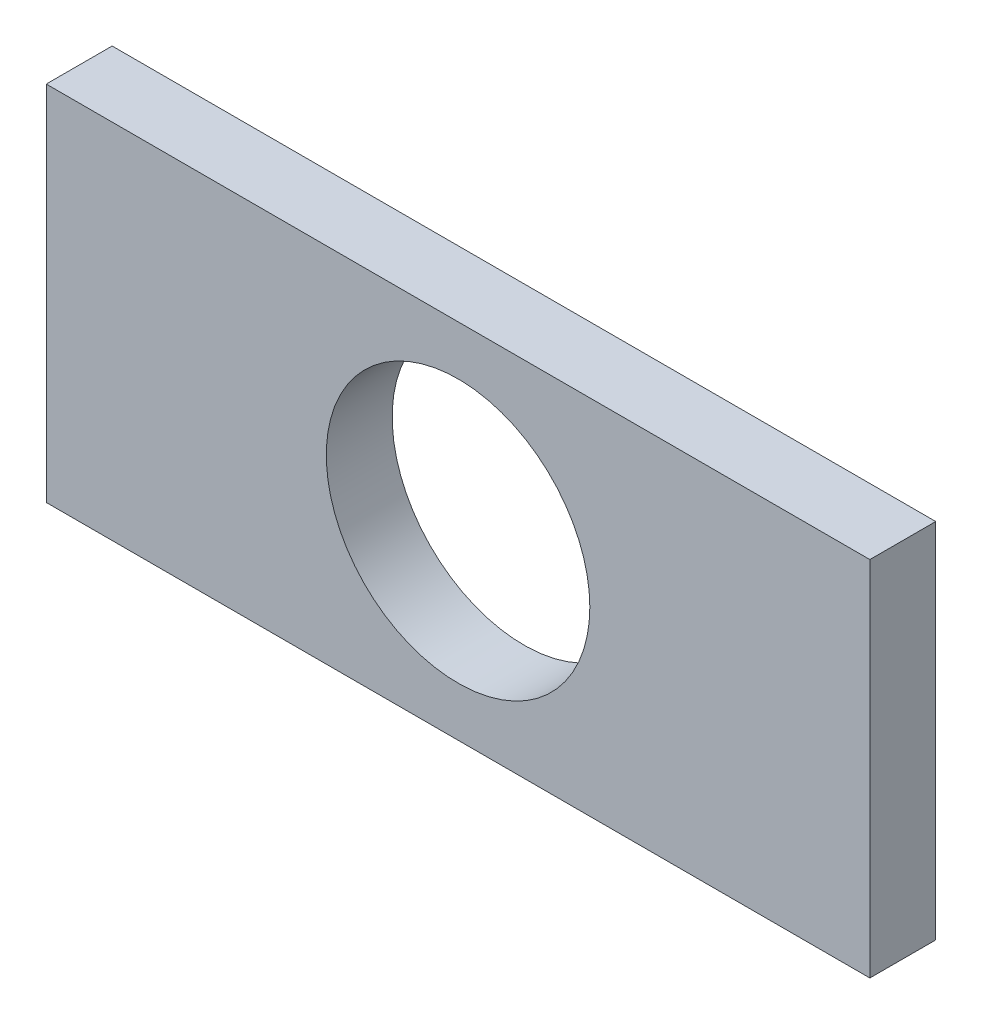
SolidWorks part; units mm, degrees
ref_plane "前视基准面" through (0, 0, 0) normal (0, 0, 1) x (1, 0, 0)
ref_plane "上视基准面" through (0, 0, 0) normal (0, 1, 0) x (1, 0, 0)
ref_plane "右视基准面" through (0, 0, 0) normal (1, 0, 0) x (0, 0, -1)
sketch "草图1" plane through (0, 0, 0) normal (0, 0, 1) x (1, 0, 0)
  line L1 (18.75, -8.25) -> (-18.75, -8.25)
  line L2 (18.75, -8.25) -> (18.75, 8.25)
  line L3 (18.75, 8.25) -> (-18.75, 8.25)
  line L4 (-18.75, -8.25) -> (-18.75, 8.25)
  line L5 (18.75, -8.25) -> (-18.75, 8.25) construction
  line L6 (18.75, 8.25) -> (-18.75, -8.25) construction
  circle A0 centre (0, 0) radius 6
  point P0 (0, 0)
extrude "凸台-拉伸1" add sketch "草图1" along normal blind 3
